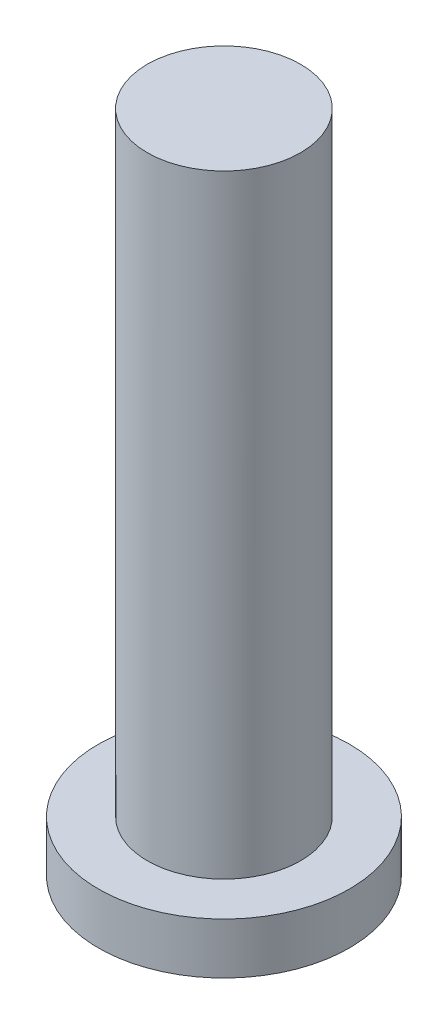
SolidWorks part; units mm, degrees
ref_plane "Plano frontal" through (0, 0, 0) normal (0, 0, 1) x (1, 0, 0)
ref_plane "Plano superior" through (0, 0, 0) normal (0, 1, 0) x (1, 0, 0)
ref_plane "Plano direito" through (0, 0, 0) normal (1, 0, 0) x (0, 0, -1)
sketch "Esboço1" plane through (0, 0, 0) normal (0, 1, 0) x (1, 0, 0)
  circle A0 centre (0, 0) radius 1.5
  dimension "D1" = 3
extrude "Ressalto-extrusão1" add sketch "Esboço1" along normal blind 12
sketch "Esboço2" plane through (0, 0, 0) normal (0, -1, 0) x (-1, 0, 0)
  circle A0 centre (0, 0) radius 2.4561
extrude "Ressalto-extrusão2" add sketch "Esboço2" along normal blind 1
